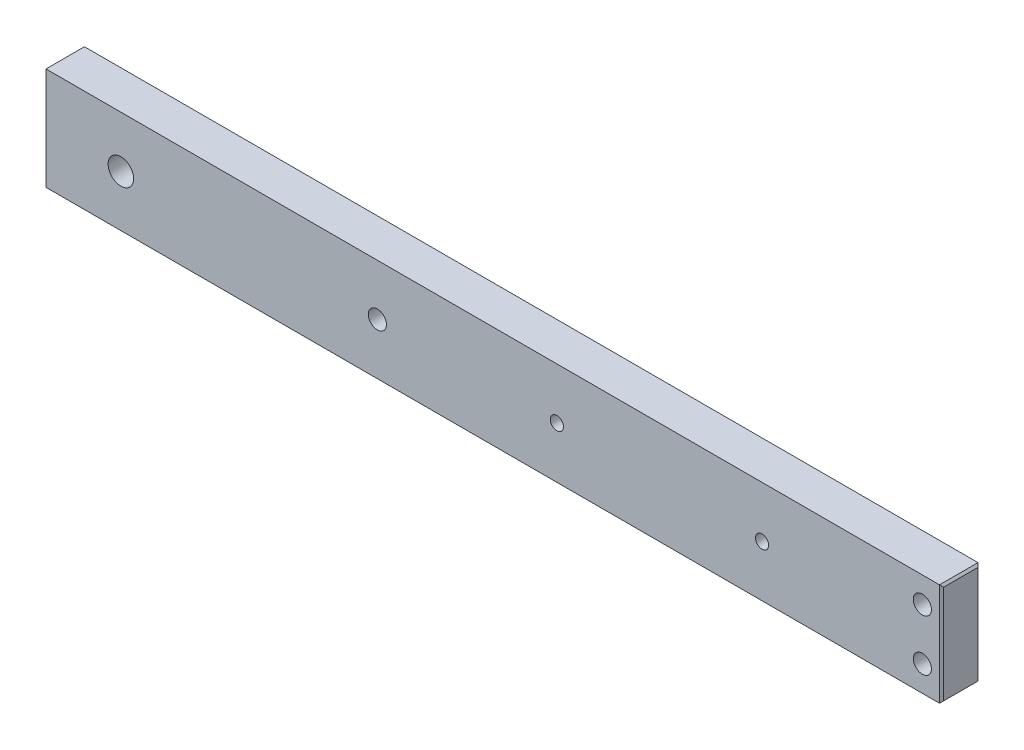
SolidWorks part; units mm, degrees
material "6061-T6 (SS)"
ref_plane "Front Plane" through (0, 0, 0) normal (0, 0, 1) x (1, 0, 0)
ref_plane "Top Plane" through (0, 0, 0) normal (0, 1, 0) x (1, 0, 0)
ref_plane "Right Plane" through (0, 0, 0) normal (1, 0, 0) x (0, 0, -1)
sketch "Sketch1" plane through (0, 0, 0) normal (0, 0, 1) x (1, 0, 0)
  line L1 (0, 0) -> (-222.25, 0)
  line L2 (0, 0) -> (0, 25.4)
  line L3 (0, 25.4) -> (-222.25, 25.4)
  line L4 (-222.25, 0) -> (-222.25, 25.4)
  dimension "D1" = 25.4
  dimension "D2" = 222.25
extrude "Boss-Extrude1" add sketch "Sketch1" along normal blind 9.525
sketch "Sketch2" plane through (0, 0, 9.525) normal (0, 0, 1) x (1, 0, 0)
  line L0 (-4.7625, 6.35) -> (-4.7625, 19.05)
  line L1 (-4.7625, 19.05) -> (-4.7625, 25.4)
  line L2 (0, 25.4) -> (-222.25, 25.4) construction
  line L3 (-4.7625, 6.35) -> (-4.7625, 0)
  line L4 (-222.25, 0) -> (0, 0) construction
  line L5 (0, 0) -> (0, 25.4) construction
  dimension "D1" = 4.7625
  dimension "D2" = 12.7
hole_wizard "#8 Clearance Hole1" positions "Sketch3" profile "Sketch4" hole size "#8" standard "ANSI Inch"
sketch "Sketch3" plane through (0, 0, 9.525) normal (0, 0, 1) x (1, 0, 0)
  point P0 (-4.7625, 6.35)
  point P3 (-4.7625, 19.05)
sketch "Sketch4" plane through (-4.7625, 6.35, 9.525) normal (1, 0, 0) x (0, -1, 0)
  line L0 (0, 0) -> (0, 26.7507)
  line L1 (0, 26.7507) -> (2.2479, 25.4)
  line L2 (2.2479, 25.4) -> (2.2479, 0)
  line L5 (2.2479, 0) -> (0, 0)
  line L10 (0, 26.7507) -> (-2.2479, 25.4) construction
  line L11 (0, -6.35) -> (0, 107.95) construction
  dimension "Hole Dia." = 4.4958
  dimension "Hole Depth" = 25.4
  dimension "Drill Angle" = 118
sketch "Sketch5" plane through (0, 0, 9.525) normal (0, 0, 1) x (1, 0, 0)
  line L0 (-222.25, 12.7) -> (-116.7098, 12.7) construction
  line L1 (-222.25, 25.4) -> (-222.25, 0) construction
  circle A0 centre (-203.2, 12.7) radius 3.1623
  point P4 (-203.2, 12.7)
  dimension "D2" = 6.3246
  dimension "D1" = 19.05
extrude "Cut-Extrude1" cut sketch "Sketch5" against normal blind 9.525 contours A0
hole_wizard "#8 Clearance Hole2" positions "Sketch8" profile "Sketch9" hole size "#8" standard "ANSI Inch"
sketch "Sketch8" plane through (0, 0, 9.525) normal (0, 0, 1) x (1, 0, 0)
  line L0 (-203.2, 12.7) -> (-139.7, 12.7)
  point P2 (-139.7, 12.7)
  dimension "D1" = 63.5
sketch "Sketch9" plane through (-139.7, 12.7, 9.525) normal (1, 0, 0) x (0, -1, 0)
  line L0 (0, 0) -> (0, 20.4007)
  line L1 (0, 20.4007) -> (2.2479, 19.05)
  line L2 (2.2479, 19.05) -> (2.2479, 0)
  line L5 (2.2479, 0) -> (0, 0)
  line L10 (0, 20.4007) -> (-2.2479, 19.05) construction
  line L11 (0, -6.35) -> (0, 107.95) construction
  dimension "Hole Dia." = 4.4958
  dimension "Hole Depth" = 19.05
  dimension "Drill Angle" = 118
chamfer "Chamfer1" distance 0.508 angle 45 8 edges at (0, 0, 4.7625) (0, 12.7, 9.525) (0, 25.4, 4.7625) (0, 12.7, 0) (-222.25, 25.4, 4.7625) (-222.25, 12.7, 9.525) (-222.25, 0, 4.7625) (-222.25, 12.7, 0)
hole_wizard "#4 Clearance Hole1" positions "Sketch10" profile "Sketch12" hole size "#4" standard "ANSI Inch" end condition through all
sketch "Sketch10" plane through (0, 0, 0) normal (0, 0, -1) x (-1, 0, 0)
  point P0 (95.25, 12.7)
  point P3 (44.45, 12.7)
sketch "Sketch12" plane through (-95.25, 12.7, 0) normal (1, 0, 0) x (0, 1, 0)
  line L0 (0, 0) -> (0, 9.525)
  line L1 (0, 9.525) -> (1.6319, 9.525)
  line L2 (1.6319, 9.525) -> (1.6319, 0)
  line L5 (1.6319, 0) -> (0, 0)
  line L11 (0, -6.35) -> (0, 107.95) construction
  dimension "Thru Hole Dia." = 3.2639
  dimension "Thru Hole Depth" = 9.525
